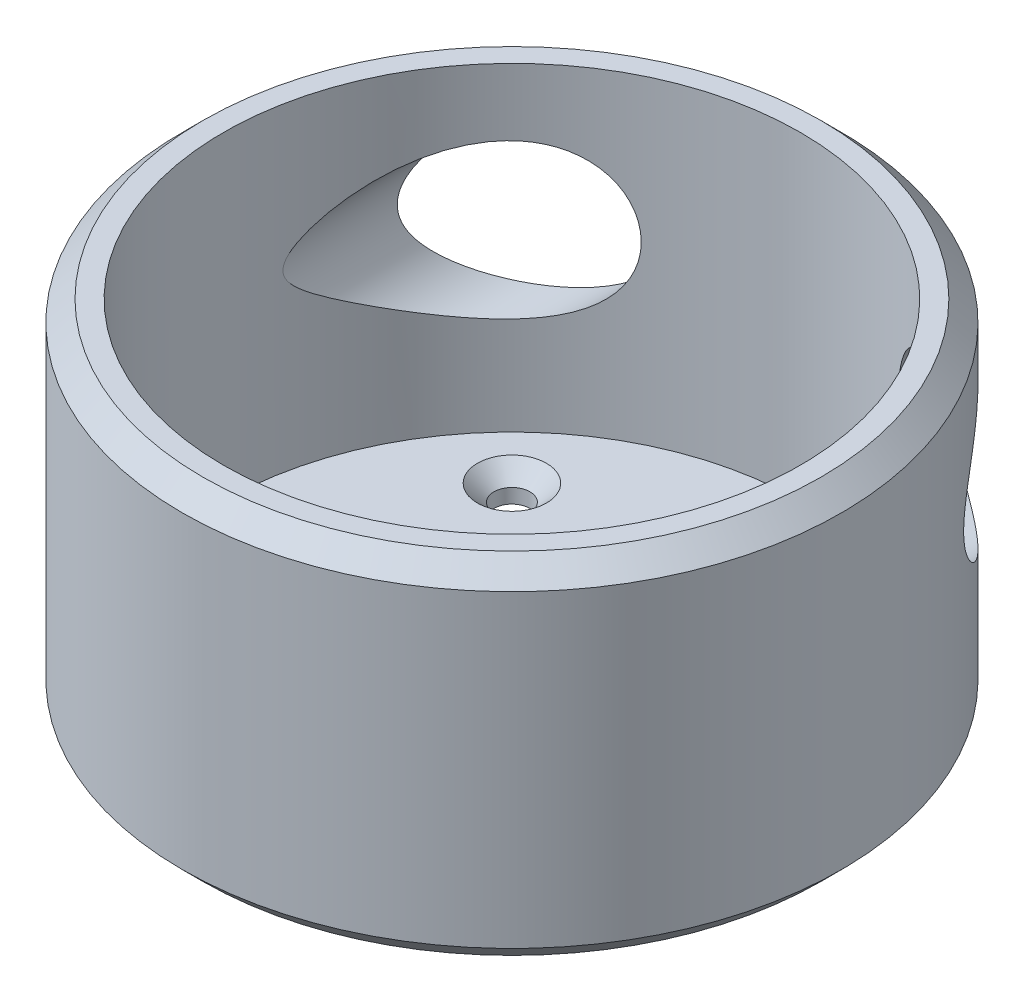
SolidWorks part; units mm, degrees
ref_plane "Front Plane" through (0, 0, 0) normal (0, 0, 1) x (1, 0, 0)
ref_plane "Top Plane" through (0, 0, 0) normal (0, 1, 0) x (1, 0, 0)
ref_plane "Right Plane" through (0, 0, 0) normal (1, 0, 0) x (0, 0, -1)
sketch "Sketch2" plane through (0, 0, 0) normal (0, 1, 0) x (1, 0, 0)
  circle A0 centre (0, 0) radius 28
  circle A1 centre (0, 0) radius 32
  dimension "D1" = 56
  dimension "D2" = 4
extrude "Boss-Extrude1" add sketch "Sketch2" along normal blind 34
sketch "Sketch3" plane through (0, 0, 0) normal (0, -1, 0) x (1, 0, 0)
  circle A0 centre (0, 0) radius 28
  circle A1 centre (0, 0) radius 28 construction
extrude "Boss-Extrude2" add sketch "Sketch3" against normal blind 3
sketch "Sketch4" plane through (0, 3, 0) normal (0, 1, 0) x (1, 0, 0)
  circle A0 centre (0, 0) radius 12.5
  dimension "D1" = 25
extrude "Cut-Extrude1" cut sketch "Sketch4" against normal blind 3
sketch "Sketch5" plane through (0, 3, 0) normal (0, 1, 0) x (1, 0, 0)
  line L1 (-15.5, 15.5) -> (15.5, 15.5) construction
  line L2 (-15.5, 15.5) -> (-15.5, -15.5) construction
  line L3 (-15.5, -15.5) -> (15.5, -15.5) construction
  line L4 (15.5, 15.5) -> (15.5, -15.5) construction
  line L5 (-15.5, 15.5) -> (15.5, -15.5) construction
  line L6 (-15.5, -15.5) -> (15.5, 15.5) construction
  circle A0 centre (0, 0) radius 2.6
  circle A1 centre (-15.5, 15.5) radius 1.75
  circle A2 centre (15.5, 15.5) radius 1.75
  circle A3 centre (-15.5, -15.5) radius 1.75
  circle A4 centre (15.5, -15.5) radius 1.75
  dimension "D1" = 5.2
  dimension "D4" = 3.5
  dimension "D5" = 3.5
  dimension "D6" = 3.5
  dimension "D7" = 3.5
  dimension "D2" = 31
  dimension "D3" = 31
extrude "Cut-Extrude2" cut sketch "Sketch5" against normal through all
chamfer "Chamfer1" distance 1.6 angle 45 4 edges at (15.5, 3, -13.75) (15.5, 3, 17.25) (-15.5, 3, 17.25) (-15.5, 3, -13.75)
chamfer "Chamfer2" distance 2 angle 45 1 edges at (0, 0, 32)
chamfer "Chamfer3" distance 2 angle 45 1 edges at (0, 34, 32)
sketch "Sketch7" plane through (0, 0, 0) normal (0, 0, 1) x (1, 0, 0)
  line L0 (-20, 20) -> (20, 20) construction
  line L1 (0, 20) -> (0, 0) construction
  circle A0 centre (-20, 20) radius 7.5
  circle A1 centre (20, 20) radius 7.5
  dimension "D1" = 15
  dimension "D2" = 15
  dimension "D3" = 40
  dimension "D4" = 20
extrude "Cut-Extrude4" cut sketch "Sketch7" against normal through all
